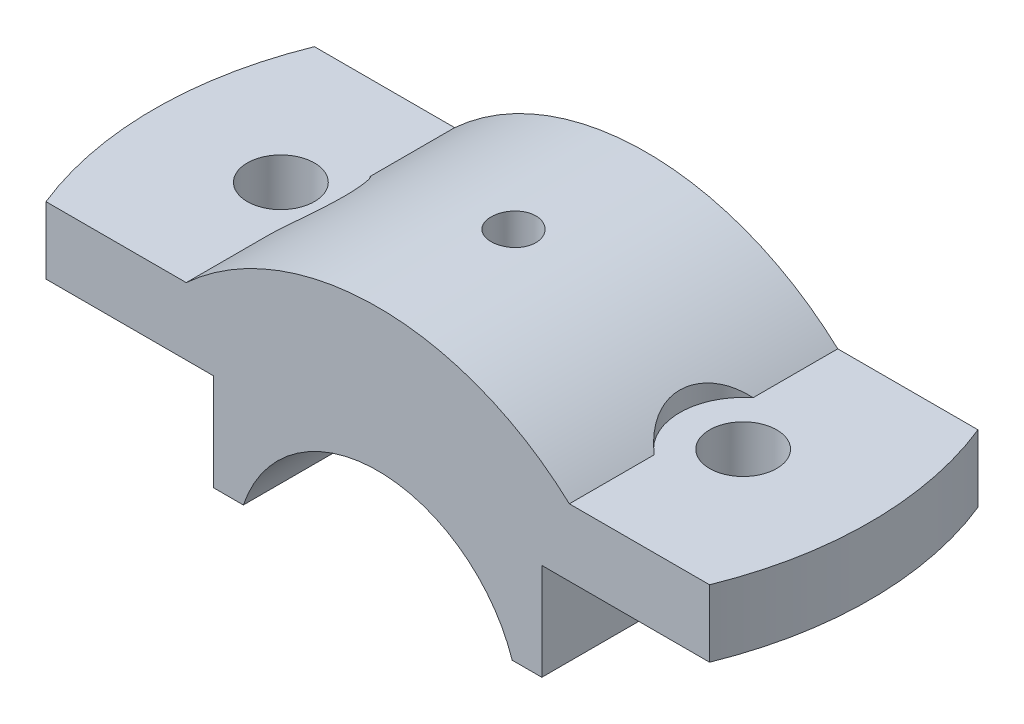
SolidWorks part; units mm, degrees
ref_plane "Front Plane" through (0, 0, 0) normal (0, 0, 1) x (1, 0, 0)
ref_plane "Top Plane" through (0, 0, 0) normal (0, 1, 0) x (1, 0, 0)
ref_plane "Right Plane" through (0, 0, 0) normal (1, 0, 0) x (0, 0, -1)
sketch "Sketch1" plane through (0, 0, 0) normal (0, 0, 1) x (1, 0, 0)
  line L0 (0, 0) -> (0, 60.593) construction
  line L1 (22, 0) -> (22, 13)
  line L2 (22, 13) -> (50, 13)
  line L3 (50, 13) -> (50, 22)
  line L4 (50, 22) -> (25.6905, 22)
  line L5 (18.0278, 0) -> (22, 0)
  line L6 (-18.0278, 0) -> (-22, 0)
  line L7 (-22, 0) -> (-22, 13)
  line L8 (-22, 13) -> (-50, 13)
  line L9 (-50, 13) -> (-50, 22)
  line L10 (-50, 22) -> (-25.6905, 22)
  arc A1 (18.0278, 0) -> (-18.0278, 0) centre (0, -6) ccw
  arc A2 (25.6905, 22) -> (-25.6905, 22) centre (0, -6) ccw
  dimension "D4" = 6
  dimension "D5" = 19
  dimension "D6" = 38
  dimension "D1" = 9
  dimension "D2" = 13
  dimension "D3" = 44
  dimension "D7" = 19
  dimension "D8" = 50
  dimension "D9" = 3.9722
extrude "Boss-Extrude1" add sketch "Sketch1" along normal mid plane 36
hole_wizard "Ø10.0mm Dowel Hole4" positions "Sketch7" profile "Sketch6" hole size "Ø10.0" standard "ANSI Metric" end condition through all
sketch "Sketch7" plane through (0, 22, 0) normal (0, 1, 0) x (1, 0, 0)
  point P0 (-31, 0)
  dimension "D1" = 31
sketch "Sketch6" plane through (-31, 22, 0) normal (1, 0, 0) x (0, 0, 1)
  line L0 (0, 0) -> (0, 22)
  line L1 (0, 22) -> (4.5, 22)
  line L2 (4.5, 22) -> (4.5, 0)
  line L5 (4.5, 0) -> (0, 0)
  line L11 (0, -6.35) -> (0, 107.95) construction
  dimension "Thru Hole Dia." = 9
  dimension "Thru Hole Depth" = 22
mirror "Mirror1" about plane through (0, 0, 0) normal (1, 0, 0) of "Ø10.0mm Dowel Hole4"
hole_wizard "CBORE for M5 Hex Head Bolt1" positions "3DSketch3" profile "Sketch13" counterbore size "M5" standard "ANSI Metric"
sketch3d "3DSketch3"
  point P0 (8.127, 31.1208, 8.1873)
  point P1 (0, 32, -0.1987)
  dimension "D1" = 0
sketch "Sketch13" plane through (0, 32, -0.1987) normal (1, 0, 0) x (0, 0, 1)
  line L0 (0, 0) -> (0, 32)
  line L1 (0, 32) -> (2.5, 32)
  line L3 (2.5, 32) -> (2.5, 13)
  line L4 (2.5, 13) -> (3, 13)
  line L5 (3, 13) -> (3, 0)
  line L7 (3, 0) -> (0, 0)
  line L11 (0, -6.35) -> (0, 107.95) construction
  dimension "Thru Hole Dia." = 5
  dimension "Thru Hole Depth" = 32
  dimension "C'Bore Dia." = 6
  dimension "C'Bore Depth" = 13
sketch "Sketch14" plane through (0, 13, 0) normal (0, -1, 0) x (1, 0, 0)
  line L0 (-44.4972, 18) -> (-50, 18)
  line L1 (-50, 18) -> (-22, 18) construction
  line L2 (-50, 18) -> (-50, -18)
  line L3 (22, -18) -> (50, -18) construction
  line L4 (-50, -18) -> (-22, -18) construction
  line L5 (-50, 18) -> (-50, -18) construction
  line L6 (-50, -18) -> (-44.3598, -18.336)
  line L7 (44.4972, 18) -> (50, 18)
  line L8 (50, 18) -> (50, -18)
  line L9 (50, 18) -> (50, -18) construction
  line L10 (50, -18) -> (44.4972, -18)
  arc A0 (-44.4972, 18) -> (-44.3598, -18.336) centre (0, 0) ccw
  arc A1 (44.4972, -18) -> (44.4972, 18) centre (0, 0) ccw
extrude "Cut-Extrude1" cut sketch "Sketch14" against normal through all
sketch "Sketch17" plane through (0, 22, 0) normal (0, 1, 0) x (1, 0, 0)
  line L0 (-25.6905, -6.6377) -> (-25.6905, 6.6377)
  line L1 (-25.6905, -18) -> (-25.6905, 18) construction
  arc A0 (-25.6905, -6.6377) -> (-25.6905, 6.6377) centre (-31, 0) ccw
  dimension "D1" = 8.5
extrude "Cut-Extrude7" cut sketch "Sketch17" along normal blind 10
mirror "Mirror3" about plane through (0, 0, 0) normal (1, 0, 0) of "Cut-Extrude7"
